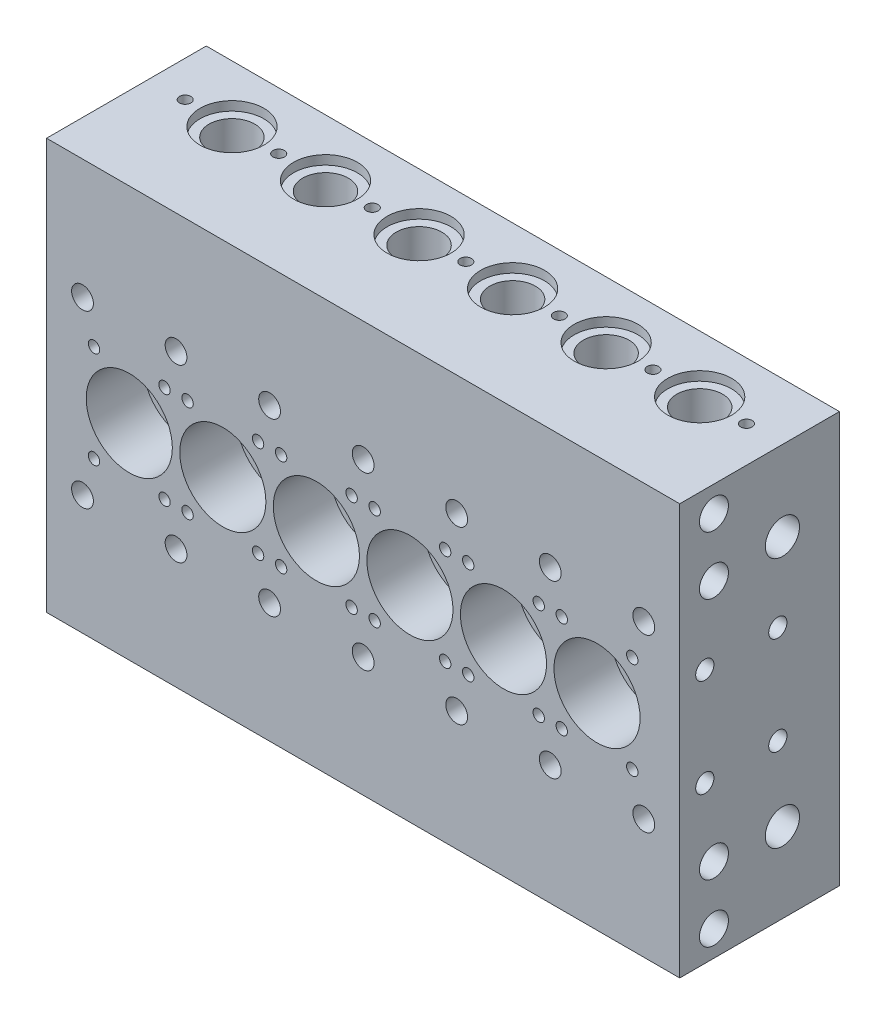
SolidWorks part; units mm, degrees
ref_plane "Front Plane" through (0, 0, 0) normal (0, 0, 1) x (1, 0, 0)
ref_plane "Top Plane" through (0, 0, 0) normal (0, 1, 0) x (1, 0, 0)
ref_plane "Right Plane" through (0, 0, 0) normal (1, 0, 0) x (0, 0, -1)
sketch "Sketch1" plane through (0, 0, 0) normal (0, 0, 1) x (1, 0, 0)
  line L1 (-277.5, -180) -> (277.5, -180)
  line L2 (-277.5, -180) -> (-277.5, 180)
  line L3 (-277.5, 180) -> (277.5, 180)
  line L4 (277.5, -180) -> (277.5, 180)
  line L5 (-277.5, -180) -> (277.5, 180) construction
  line L6 (-277.5, 180) -> (277.5, -180) construction
  point P0 (0, 0)
  dimension "D1" = 555
  dimension "D2" = 360
extrude "Boss-Extrude1" add sketch "Sketch1" along normal blind 140
sketch "Sketch2" plane through (0, 0, 140) normal (0, 0, 1) x (1, 0, 0)
  line L0 (-277.5, -180) -> (277.5, -180) construction
  line L1 (-277.5, 180) -> (-277.5, -180) construction
  circle A0 centre (-205, 0) radius 22.5
  dimension "D1" = 180
  dimension "D3" = 45
  dimension "D2" = 72.5
extrude "Cut-Extrude1" cut sketch "Sketch2" against normal up to next (140 mm away)
sketch "Sketch3" plane through (0, 0, 140) normal (0, 0, 1) x (1, 0, 0)
  circle A0 centre (-205, 0) radius 37.75
  dimension "D1" = 75.5
extrude "Cut-Extrude2" cut sketch "Sketch3" against normal blind 50
sketch "Sketch4" plane through (0, 0, 0) normal (0, 0, -1) x (-1, 0, 0)
  circle A0 centre (205, 0) radius 28
  dimension "D1" = 56
extrude "Cut-Extrude3" cut sketch "Sketch4" against normal blind 8
pattern_linear "LPattern1" count 6 spacing 82 along (1, 0, 0) of "Cut-Extrude1", "Cut-Extrude3", "Cut-Extrude2"
sketch "Sketch5" plane through (0, 0, 140) normal (0, 0, 1) x (1, 0, 0)
  circle A0 centre (-235.9, 42.5) radius 5
  circle A1 centre (-205, 0) radius 37.75 construction
  dimension "D1" = 10
  dimension "D2" = 42.5
  dimension "D3" = 30.9
extrude "Cut-Extrude4" cut sketch "Sketch5" against normal blind 20
pattern_linear "LPattern2" count 2 spacing 61.8 along (1, 0, 0) count 2 spacing 84.9 along (0, -1, 0) of "Cut-Extrude4"
pattern_linear "LPattern3" count 6 spacing 82 along (1, 0, 0) of "Cut-Extrude4", "LPattern2"
sketch "Sketch6" plane through (0, 0, 140) normal (0, 0, 1) x (1, 0, 0)
  circle A0 centre (-246, 75) radius 9.55
  circle A1 centre (-205, 0) radius 37.75 construction
  dimension "D1" = 19.1
  dimension "D2" = 75
  dimension "D3" = 41
extrude "Cut-Extrude5" cut sketch "Sketch6" against normal up to next (140 mm away)
pattern_linear "LPattern4" count 2 spacing 150 along (0, -1, 0) count 7 spacing 82 along (1, 0, 0) of "Cut-Extrude5"
sketch "Sketch7" plane through (277.5, 0, 0) normal (1, 0, 0) x (0, 0, -1)
  line L0 (-140, -180) -> (-140, 180) construction
  line L1 (-140, -180) -> (0, -180) construction
  line L2 (-140, 180) -> (0, 180) construction
  circle A0 centre (-110, -157.5) radius 12.7
  circle A1 centre (-110, -106.5) radius 12.7
  circle A2 centre (-50, -110) radius 15
  circle A3 centre (-110, 157.5) radius 12.7
  circle A4 centre (-50, 110) radius 15
  circle A5 centre (-110, 106.5) radius 12.7
  point P16 (0, 0)
  point P19 (0, 0)
  point P20 (0, 0)
  dimension "D1" = 30
  dimension "D3" = 25.4
  dimension "D4" = 25.4
  dimension "D5" = 30
  dimension "D9" = 25.4
  dimension "D10" = 25.4
  dimension "D11" = 30
  dimension "D2" = 22.5
  dimension "D6" = 73.5
  dimension "D7" = 70
  dimension "D8" = 90
  dimension "D12" = 22.5
  dimension "D13" = 73.5
  dimension "D14" = 70
extrude "Cut-Extrude6" cut sketch "Sketch7" against normal through all
sketch "Sketch8" plane through (277.5, 0, 0) normal (1, 0, 0) x (0, 0, -1)
  line L0 (-140, -180) -> (0, -180) construction
  line L1 (-140, -180) -> (-140, 180) construction
  circle A0 centre (-118, -43) radius 8
  dimension "D1" = 16
  dimension "D2" = 137
  dimension "D3" = 22
extrude "Cut-Extrude7" cut sketch "Sketch8" against normal blind 23
pattern_linear "LPattern5" count 2 spacing 64 along (0, 0, -1) count 2 spacing 86 along (0, 1, 0) of "Cut-Extrude7"
sketch "Sketch9" plane through (-277.5, 0, 0) normal (-1, 0, 0) x (0, 0, 1)
  line L0 (140, 180) -> (0, 180) construction
  line L1 (140, 180) -> (140, -180) construction
  circle A0 centre (118, 43) radius 8
  dimension "D1" = 16
  dimension "D2" = 137
  dimension "D3" = 22
extrude "Cut-Extrude8" cut sketch "Sketch9" against normal blind 23
pattern_linear "LPattern6" count 2 spacing 64 along (0, 0, -1) count 2 spacing 86 along (0, -1, 0) of "Cut-Extrude8"
sketch "Sketch10" plane through (0, 180, 0) normal (0, 1, 0) x (1, 0, 0)
  line L0 (277.5, -140) -> (-277.5, -140) construction
  line L1 (-277.5, -140) -> (-277.5, 0) construction
  circle A0 centre (-205, -50) radius 28
  dimension "D1" = 90
  dimension "D3" = 56
  dimension "D2" = 72.5
extrude "Cut-Extrude9" cut sketch "Sketch10" against normal blind 8
sketch "Sketch11" plane through (0, 172, 0) normal (0, 1, 0) x (1, 0, 0)
  circle A0 centre (-205, -50) radius 20
  dimension "D1" = 40
extrude "Cut-Extrude10" cut sketch "Sketch11" against normal blind 139
sketch "Sketch12" plane through (0, 33, 0) normal (0, 1, 0) x (1, 0, 0)
  circle A0 centre (-205, -50) radius 5
  dimension "D1" = 10
extrude "Cut-Extrude11" cut sketch "Sketch12" against normal blind 20
sketch "Sketch13" plane through (0, -180, 0) normal (0, -1, 0) x (1, 0, 0)
  line L0 (-277.5, 140) -> (-277.5, 0) construction
  line L1 (-277.5, 140) -> (277.5, 140) construction
  circle A0 centre (-205, 50) radius 28
  dimension "D1" = 56
  dimension "D2" = 72.5
  dimension "D3" = 90
extrude "Cut-Extrude12" cut sketch "Sketch13" against normal blind 8
sketch "Sketch14" plane through (0, -172, 0) normal (0, -1, 0) x (1, 0, 0)
  circle A0 centre (-205, 50) radius 20
  dimension "D1" = 40
extrude "Cut-Extrude13" cut sketch "Sketch14" against normal blind 139
sketch "Sketch15" plane through (0, -33, 0) normal (0, -1, 0) x (1, 0, 0)
  circle A0 centre (-205, 50) radius 16
  dimension "D1" = 32
extrude "Cut-Extrude14" cut sketch "Sketch15" against normal blind 20
pattern_linear "LPattern7" count 6 spacing 82 along (1, 0, 0) of "Cut-Extrude9", "Cut-Extrude14", "Cut-Extrude13", "Cut-Extrude12", "Cut-Extrude11", "Cut-Extrude10"
sketch "Sketch16" plane through (0, 180, 0) normal (0, 1, 0) x (1, 0, 0)
  line L0 (277.5, -140) -> (-277.5, -140) construction
  circle A0 centre (-246, -50) radius 5
  circle A1 centre (-205, -50) radius 28 construction
  dimension "D1" = 41
  dimension "D3" = 10
  dimension "D2" = 90
extrude "Cut-Extrude15" cut sketch "Sketch16" against normal blind 20
pattern_linear "LPattern8" count 7 spacing 82 along (1, 0, 0) of "Cut-Extrude15"
sketch "Sketch17" plane through (0, -180, 0) normal (0, -1, 0) x (1, 0, 0)
  circle A0 centre (-246, 50) radius 5
  circle A1 centre (-205, 50) radius 28 construction
  dimension "D1" = 90
  dimension "D2" = 41
  dimension "D3" = 10
extrude "Cut-Extrude16" cut sketch "Sketch17" against normal blind 20
pattern_linear "LPattern9" count 7 spacing 82 along (1, 0, 0) of "Cut-Extrude16"
